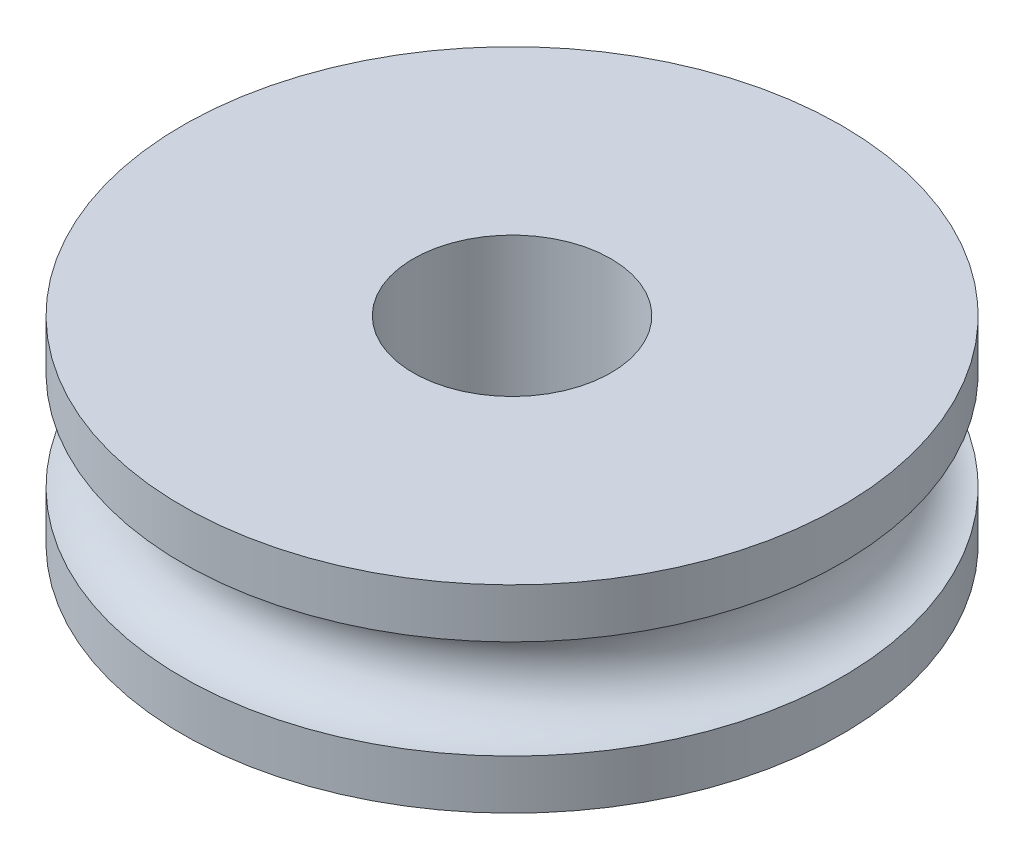
SolidWorks part; units mm, degrees
ref_plane "Front Plane" through (0, 0, 0) normal (0, 0, 1) x (1, 0, 0)
ref_plane "Top Plane" through (0, 0, 0) normal (0, 1, 0) x (1, 0, 0)
ref_plane "Right Plane" through (0, 0, 0) normal (1, 0, 0) x (0, 0, -1)
sketch "Sketch1" plane through (0, 0, 0) normal (1, 0, 0) x (0, 0, -1)
  line L1 (-1.5, 1.5) -> (-5, 1.5)
  line L2 (-5, 1.5) -> (-5, 0.75)
  line L3 (-5, -0.75) -> (-5, -1.5)
  line L4 (-5, -1.5) -> (-1.5, -1.5)
  line L6 (0, 0) -> (0, 5.0208) construction
  line L7 (-1.5, 0) -> (-11.5024, 0) construction
  line L8 (-1.5, 1.5) -> (-1.5, -1.5)
  line L9 (0, 0) -> (0, -3.9554) construction
  line L10 (0, 0) -> (3.6276, 0) construction
  arc A0 (-5, 0.75) -> (-5, -0.75) centre (-5, 0) cw
  dimension "D5" = 1.5
  dimension "D2" = 3
  dimension "D1" = 1.5
  dimension "D3" = 5
revolve "Revolve1" add sketch "Sketch1" angle 360 about L6
sketch "Sketch2" [suppressed] plane through (0, 0, 0) normal (1, 0, 0) x (0, 0, -1)
  line L0 (0, -3.0671) -> (0, 3.2316) construction
  line L1 (5.7825, 0) -> (-7.0668, 0) construction
  line L2 (-6.9266, 0) -> (2.4055, 0) construction
  line L10 (-1.95, 2) -> (-6.5, 2)
  line L11 (-6.5, 2) -> (-6.5, 1)
  line L12 (-6.5, -1) -> (-6.5, -2)
  line L13 (-6.5, -2) -> (-1.95, -2)
  line L14 (-1.95, -2) -> (-1.95, 2)
  arc A2 (-6.5, -1) -> (-6.5, 1) centre (-6.751, 0) ccw
  point P15 (-5.72, 0)
  dimension "D2" = 6.5
  dimension "D1" = 1.95
  dimension "D3" = 4
  dimension "D4" = 1
  dimension "D5" = 1
  dimension "D6" = 0
  dimension "D7" = 11.44
revolve "Revolve2" [suppressed] add sketch "Sketch2" angle 360 about L0
equation "\"InnerDiaBig\"= 4mm"
equation "\"InnerDiaSmall\"=3"
equation "\"D1@Sketch1\" = \"InnerDiaSmall\"/2"
